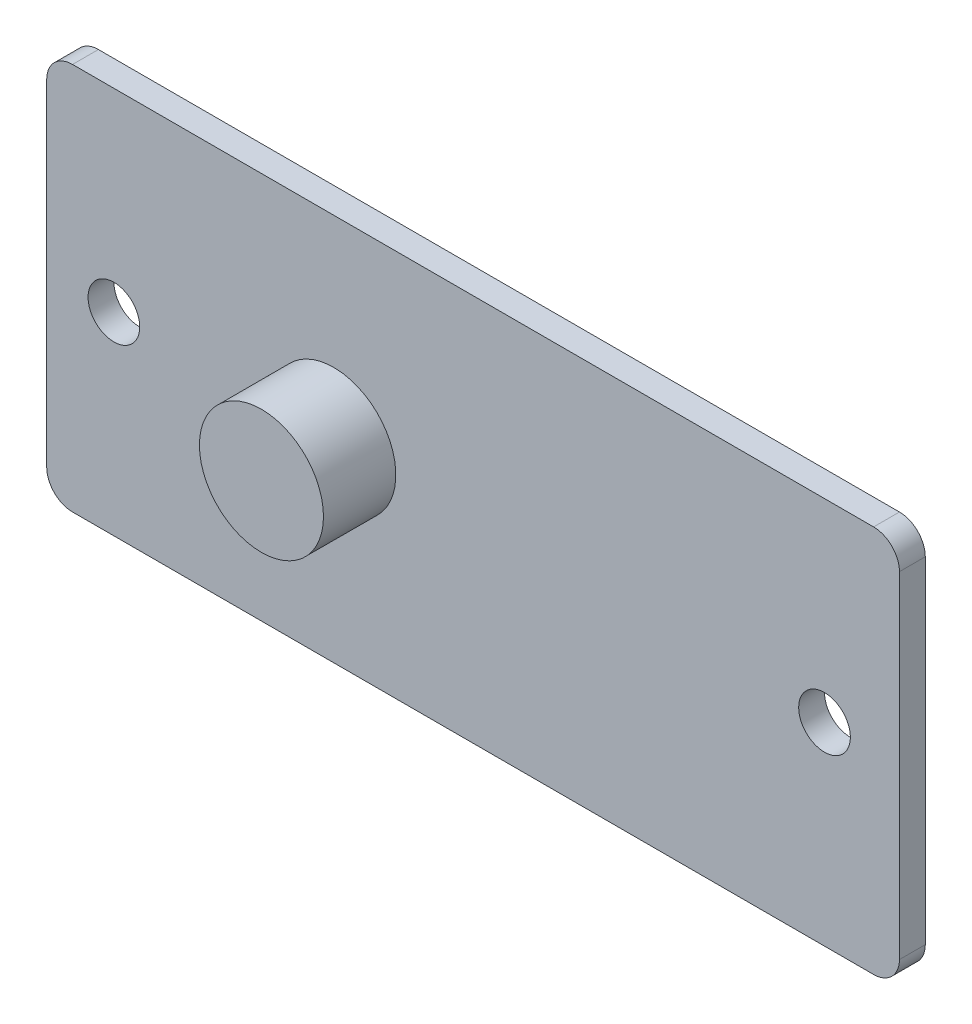
SolidWorks part; units mm, degrees
ref_plane "Front Plane" through (0, 0, 0) normal (0, 0, 1) x (1, 0, 0)
ref_plane "Top Plane" through (0, 0, 0) normal (0, 1, 0) x (1, 0, 0)
ref_plane "Right Plane" through (0, 0, 0) normal (1, 0, 0) x (0, 0, -1)
sketch "Sketch1" plane through (0, 0, 0) normal (0, 0, 1) x (1, 0, 0)
  line L0 (-16.5, 0) -> (-13.9, 0) construction
  line L1 (-15.5, 7.5) -> (15.5, 7.5)
  line L2 (-16.5, 6.5) -> (-16.5, -6.5)
  line L3 (-15.5, -7.5) -> (15.5, -7.5)
  line L4 (16.5, 6.5) -> (16.5, -6.5)
  line L5 (-16.5, 7.5) -> (16.5, -7.5) construction
  line L6 (-16.5, -7.5) -> (16.5, 7.5) construction
  arc A0 (15.5, 7.5) -> (16.5, 6.5) centre (15.5, 6.5) cw
  arc A1 (15.5, -7.5) -> (16.5, -6.5) centre (15.5, -6.5) ccw
  arc A2 (-16.5, -6.5) -> (-15.5, -7.5) centre (-15.5, -6.5) ccw
  arc A3 (-15.5, 7.5) -> (-16.5, 6.5) centre (-15.5, 6.5) ccw
  circle A4 centre (-13.9, 0) radius 1
  circle A5 centre (13.6, 0) radius 1
  point P0 (0, 0)
  dimension "D3" = 1
  dimension "D5" = 2
  dimension "D1" = 33
  dimension "D2" = 15
  dimension "D4" = 2.6
  dimension "D6" = 27.5
extrude "Boss-Extrude1" add sketch "Sketch1" along normal blind 1
sketch "Sketch2" plane through (0, 0, 1) normal (0, 0, 1) x (1, 0, 0)
  line L0 (-16.5, 0) -> (-5.39, 0) construction
  line L1 (-16.5, 6.5) -> (-16.5, -6.5) construction
  circle A0 centre (-5.39, 0) radius 2.4
  dimension "D2" = 4.8
  dimension "D1" = 11.11
extrude "Boss-Extrude2" add sketch "Sketch2" along normal blind 2.8
